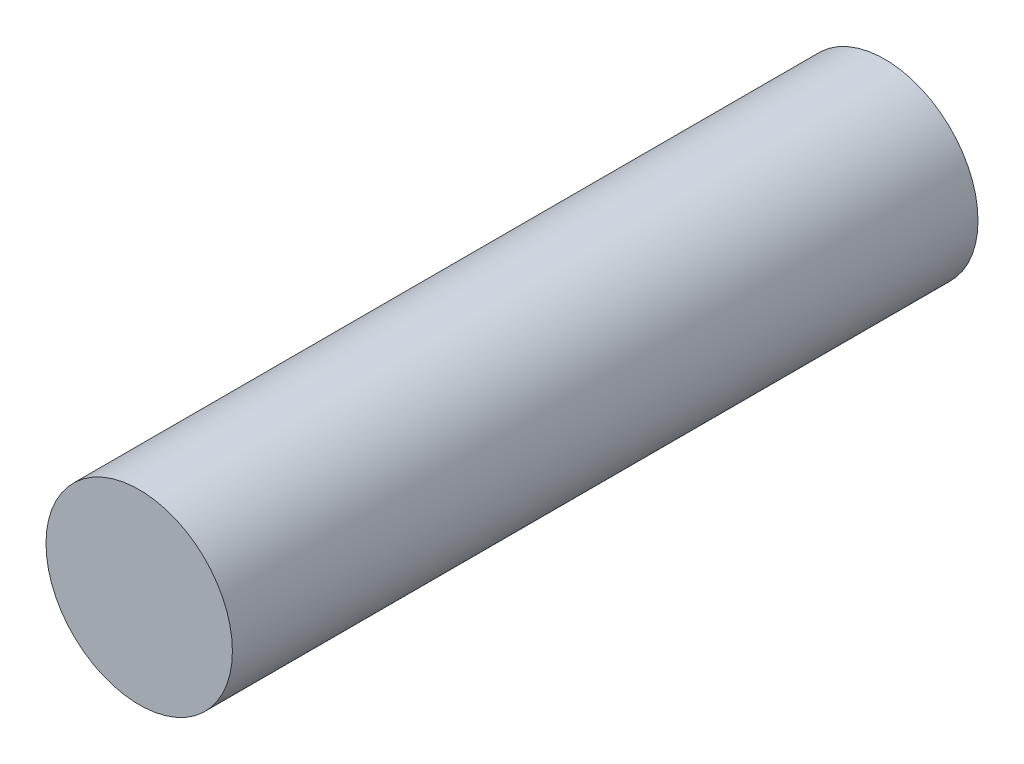
SolidWorks part; units mm, degrees
ref_plane "Front Plane" through (0, 0, 0) normal (0, 0, 1) x (1, 0, 0)
ref_plane "Top Plane" through (0, 0, 0) normal (0, 1, 0) x (1, 0, 0)
ref_plane "Right Plane" through (0, 0, 0) normal (1, 0, 0) x (0, 0, -1)
sketch "Sketch1" plane through (0, 0, 0) normal (0, 0, 1) x (1, 0, 0)
  circle A0 centre (0, 0) radius 3.75
  dimension "D1" = 7.5
extrude "Boss-Extrude1" add sketch "Sketch1" along normal blind 30
